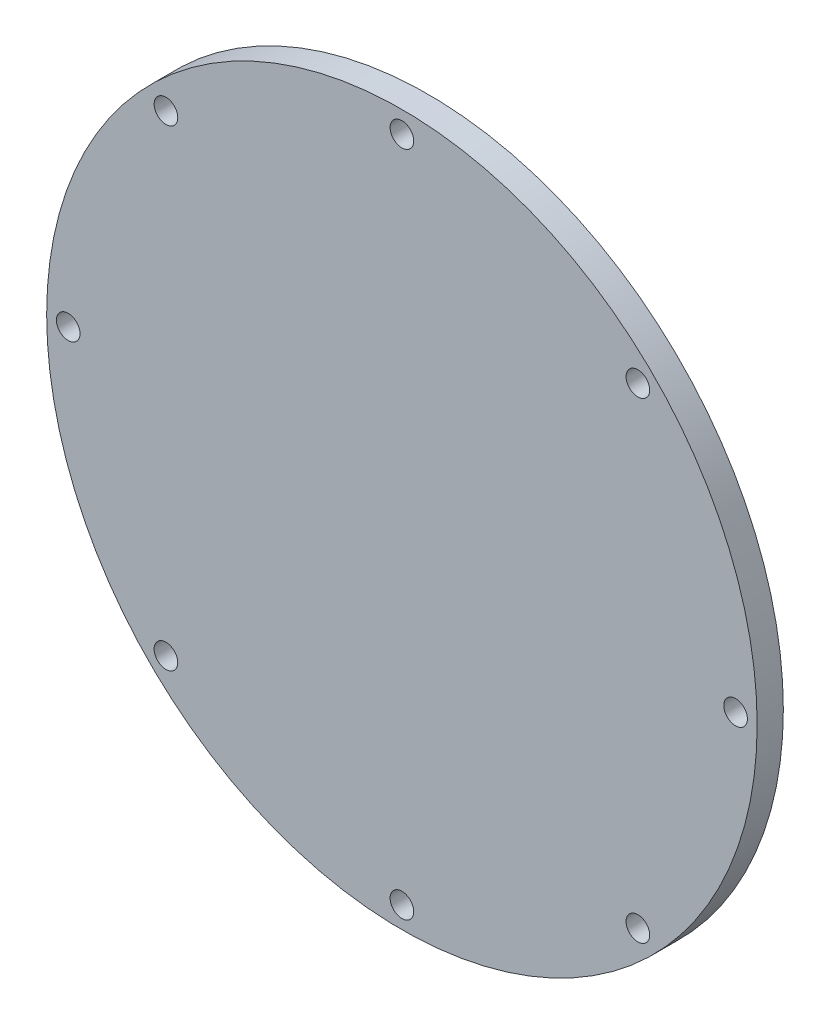
SolidWorks part; units mm, degrees
ref_plane "Front Plane" through (0, 0, 0) normal (0, 0, 1) x (1, 0, 0)
ref_plane "Top Plane" through (0, 0, 0) normal (0, 1, 0) x (1, 0, 0)
ref_plane "Right Plane" through (0, 0, 0) normal (1, 0, 0) x (0, 0, -1)
sketch "Sketch1" plane through (0, 0, 0) normal (0, 0, 1) x (1, 0, 0)
  line L7 (0, -71.3867) -> (50.478, -50.478) construction
  line L8 (50.478, -50.478) -> (71.3867, 0) construction
  line L9 (71.3867, 0) -> (50.478, 50.478) construction
  line L10 (50.478, 50.478) -> (0, 71.3867) construction
  line L11 (0, 71.3867) -> (-50.478, 50.478) construction
  line L12 (-50.478, 50.478) -> (-71.3867, 0) construction
  line L13 (-71.3867, 0) -> (-50.478, -50.478) construction
  line L14 (-50.478, -50.478) -> (0, -71.3867) construction
  circle A0 centre (0, 0) radius 76
  circle A1 centre (0, 0) radius 65.9527 construction
  point P15 (50.478, 50.478)
  point P20 (71.3867, 0)
  point P21 (0, 71.3867)
  point P22 (50.478, -50.478)
  point P23 (0, -71.3867)
  point P24 (-50.478, -50.478)
  point P25 (-71.3867, 0)
  point P26 (-50.478, 50.478)
  dimension "D2" = 152
  dimension "D1" = 142.7734
extrude "Boss-Extrude1" add sketch "Sketch1" along normal blind 5.6
sketch "Sketch3" plane through (0, 0, 0) normal (0, 0, -1) x (-1, 0, 0)
  point P13 (-50.478, 50.478)
  point P16 (0, 71.3867)
  point P19 (50.478, 50.478)
  point P22 (71.3867, 0)
  point P25 (50.478, -50.478)
  point P28 (0, -71.3867)
  point P31 (-50.478, -50.478)
  point P34 (-71.3867, 0)
hole_wizard "#8 (0.199) Diameter Hole1" positions "Sketch3" profile "Sketch4" hole size "#8" standard "ANSI Inch"
sketch "Sketch4" plane through (50.478, 50.478, 0) normal (1, 0, 0) x (0, 1, 0)
  line L0 (0, 0) -> (0, 10)
  line L1 (0, 10) -> (2.5273, 8.4814)
  line L2 (2.5273, 8.4814) -> (2.5273, 0)
  line L5 (2.5273, 0) -> (0, 0)
  line L10 (0, 10) -> (-2.5273, 8.4814) construction
  line L11 (0, -6.35) -> (0, 107.95) construction
  dimension "Hole Dia." = 5.0546
  dimension "Hole Depth" = 10
  dimension "Drill Angle" = 118
